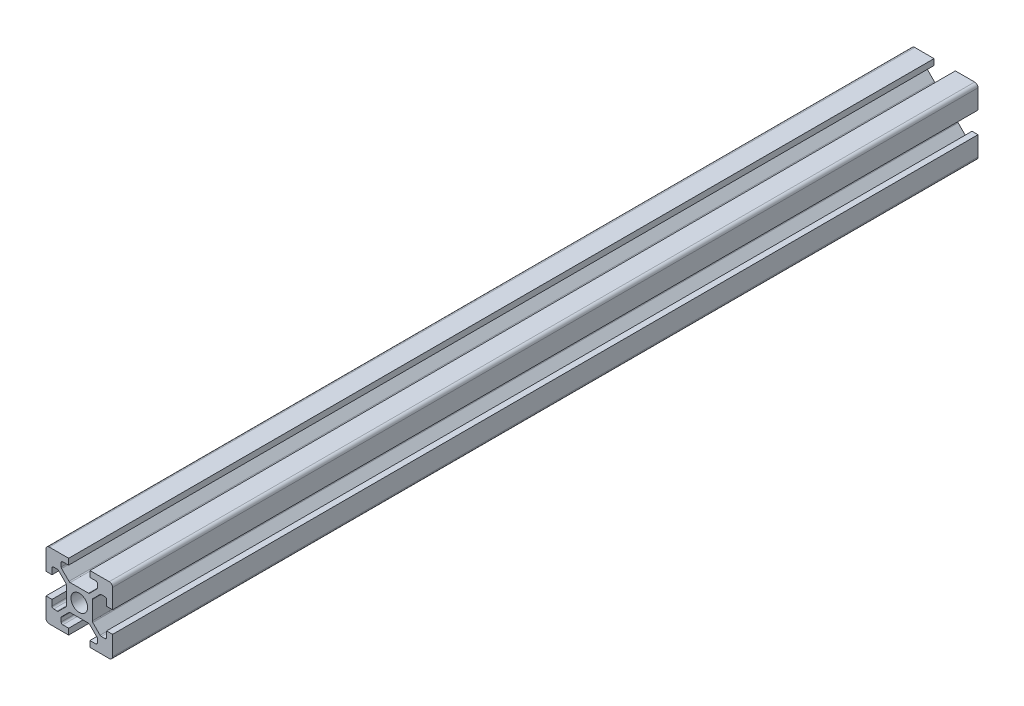
SolidWorks part; units mm, degrees
material "1060 Alloy"
ref_plane "Front Plane" through (0, 0, 0) normal (0, 0, 1) x (1, 0, 0)
ref_plane "Top Plane" through (0, 0, 0) normal (0, 1, 0) x (1, 0, 0)
ref_plane "Right Plane" through (0, 0, 0) normal (1, 0, 0) x (0, 0, -1)
sketch "Sketch1" plane through (0, 0, 0) normal (0, 0, 1) x (1, 0, 0)
  line L0 (20, 0) -> (-8.059, 28.059) construction
  line L1 (0, 0) -> (6.8, 0)
  line L2 (0, 0) -> (0, 6.8)
  line L3 (0, 20) -> (6.8, 20)
  line L4 (20, 0) -> (20, 6.8)
  line L5 (6.8, 20) -> (6.8, 18.2)
  line L6 (20, 20) -> (8.2322, 8.2322) construction
  line L7 (12.95, 6.1) -> (7.05, 6.1)
  line L8 (13.9, 7.05) -> (13.9, 12.95)
  line L9 (12.95, 13.9) -> (7.05, 13.9)
  line L10 (6.1, 7.05) -> (6.1, 12.95)
  line L11 (13.9, 6.1) -> (6.1, 13.9) construction
  line L12 (13.9, 13.9) -> (6.1, 6.1) construction
  line L13 (4.55, 16.4) -> (7.05, 13.9)
  line L14 (13.2, 18.2) -> (13.2, 20)
  line L15 (1.8, 6.8) -> (0, 6.8)
  line L16 (0, 13.2) -> (0, 20)
  line L17 (0, 13.2) -> (1.8, 13.2)
  line L18 (10, 10) -> (10, 13.9) construction
  line L19 (16.4, 4.55) -> (13.9, 7.05)
  line L20 (4.55, 16.4) -> (4.55, 18.2)
  line L21 (4.55, 18.2) -> (6.8, 18.2)
  line L22 (13.2, 18.2) -> (15.45, 18.2)
  line L23 (15.45, 18.2) -> (15.45, 16.4)
  line L24 (15.45, 16.4) -> (12.95, 13.9)
  line L25 (16.4, 4.55) -> (18.2, 4.55)
  line L26 (18.2, 4.55) -> (18.2, 6.8)
  line L27 (20, 6.8) -> (18.2, 6.8)
  line L28 (18.2, 13.2) -> (20, 13.2)
  line L29 (18.2, 13.2) -> (18.2, 15.45)
  line L30 (18.2, 15.45) -> (16.4, 15.45)
  line L31 (16.4, 15.45) -> (13.9, 12.95)
  line L32 (1.8, 4.55) -> (3.6, 4.55)
  line L33 (3.6, 15.45) -> (6.1, 12.95)
  line L34 (3.6, 15.45) -> (1.8, 15.45)
  line L35 (1.8, 15.45) -> (1.8, 13.2)
  line L38 (3.6, 4.55) -> (6.1, 7.05)
  line L39 (1.8, 6.8) -> (1.8, 4.55)
  line L40 (15.45, 3.6) -> (12.95, 6.1)
  line L41 (4.55, 3.6) -> (7.05, 6.1)
  line L42 (4.55, 1.8) -> (4.55, 3.6)
  line L43 (6.8, 1.8) -> (4.55, 1.8)
  line L44 (6.8, 1.8) -> (6.8, 0)
  line L45 (15.45, 3.6) -> (15.45, 1.8)
  line L46 (15.45, 1.8) -> (13.2, 1.8)
  line L47 (13.2, 0) -> (13.2, 1.8)
  line L48 (13.2, 20) -> (20, 20)
  line L49 (20, 13.2) -> (20, 20)
  line L50 (13.2, 0) -> (20, 0)
  line L51 (6.1, 6.1) -> (-5.5045, -5.5045) construction
  circle A0 centre (10, 10) radius 2.5
  point P25 (10, 16.4)
  point P39 (13.2, 19.1)
  point P46 (0.9, 6.8)
  dimension "D3" = 5
  dimension "D2" = 20
  dimension "D4" = 7.8
  dimension "D5" = 7.8
  dimension "D6" = 6.8
  dimension "D7" = 6.8
  dimension "D8" = 1.8
  dimension "D9" = 10.9
  dimension "D10" = 1.8
  dimension "D11" = 10.9
  dimension "D12" = 20
extrude "Boss-Extrude1" add sketch "Sketch1" along normal blind 300 contours L47 L50 L4 L27 L26 L25 L19 L8 L31 L30 L29 L28 L49 L48 L14 L22 L23 L24 L9 L13 L20 L21 L5 L3 L16 L17 L35 L34 L33 L10 L38 L32 L39 L15 L2 L1 L44 L43 L42 L41 L7 L40 L45 L46 A0
fillet "Fillet1" radius 1 4 edges at (20, 20, 150) (20, 0, 150) (0, 0, 150) (0, 20, 150)
fillet "Fillet2" radius 0.5 6 edges at (4.55, 18.2, 150) (4.55, 16.4, 150) (7.05, 13.9, 150) (15.45, 18.2, 150) (15.45, 16.4, 150) (12.95, 13.9, 150)
fillet "Fillet3" radius 0.5 6 edges at (18.2, 15.45, 150) (16.4, 15.45, 150) (13.9, 12.95, 150) (18.2, 4.55, 150) (13.9, 7.05, 150) (16.4, 4.55, 150)
fillet "Fillet4" radius 0.5 6 edges at (1.8, 15.45, 150) (3.6, 15.45, 150) (6.1, 12.95, 150) (3.6, 4.55, 150) (1.8, 4.55, 150) (6.1, 7.05, 150)
fillet "Fillet5" radius 0.5 6 edges at (7.05, 6.1, 150) (4.55, 3.6, 150) (4.55, 1.8, 150) (15.45, 1.8, 150) (15.45, 3.6, 150) (12.95, 6.1, 150)
sketch "Sketch4" plane through (0, 0, 0) normal (0, 0, -1) x (-1, 0, 0)
  line L1 (55.7447, -48.755) -> (-29.3857, -48.755)
  line L2 (55.7447, -48.755) -> (55.7447, 27.7374)
  line L3 (55.7447, 27.7374) -> (-29.3857, 27.7374)
  line L4 (-29.3857, -48.755) -> (-29.3857, 27.7374)
  line L5 (55.7447, -48.755) -> (-29.3857, 27.7374) construction
  line L6 (55.7447, 27.7374) -> (-29.3857, -48.755) construction
  point P0 (13.1795, -10.5088)
extrude "Cut-Extrude4" cut sketch "Sketch4" against normal blind 40
